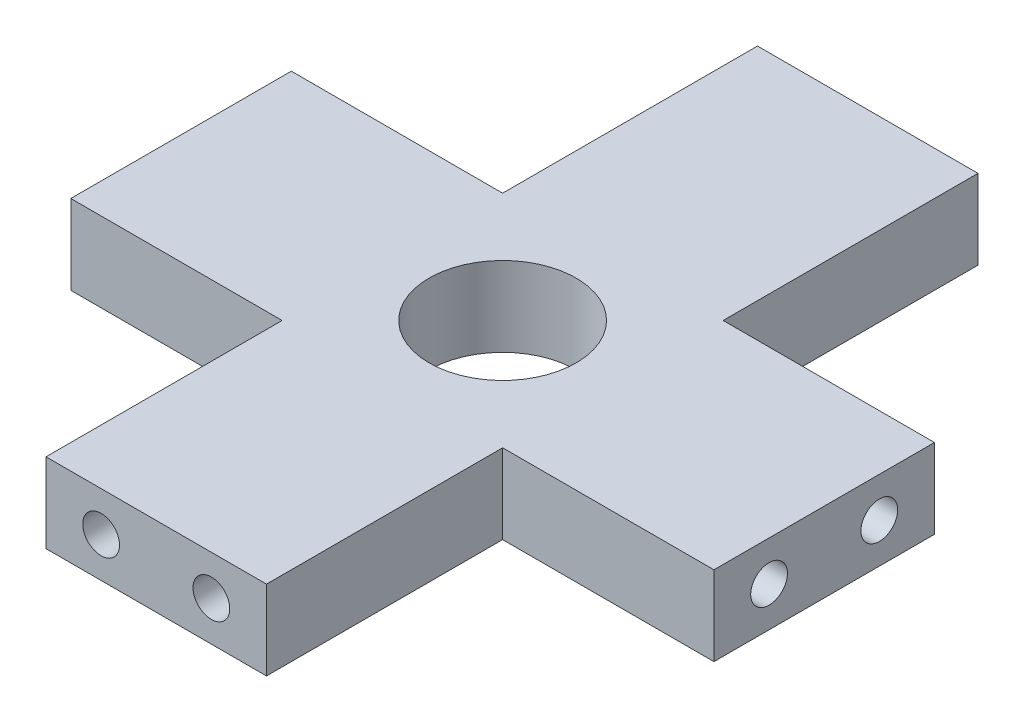
SolidWorks part; units mm, degrees
ref_plane "Front Plane" through (0, 0, 0) normal (0, 0, 1) x (1, 0, 0)
ref_plane "Top Plane" through (0, 0, 0) normal (0, 1, 0) x (1, 0, 0)
ref_plane "Right Plane" through (0, 0, 0) normal (1, 0, 0) x (0, 0, -1)
sketch "Sketch2" plane through (0, 0, 0) normal (0, 1, 0) x (1, 0, 0)
  line L0 (-11.5, 18.85) -> (23.5, 18.85) construction
  line L1 (0, 0) -> (12, 0)
  line L2 (0, 0) -> (0, 12.85)
  line L3 (0, 38.72) -> (12, 38.72)
  line L4 (12, 0) -> (12, 12.85)
  line L5 (6, 0) -> (6, 38.72) construction
  line L6 (-11.5, 24.85) -> (0, 24.85)
  line L7 (-11.5, 24.85) -> (-11.5, 12.85)
  line L8 (-11.5, 12.85) -> (0, 12.85)
  line L9 (23.5, 24.85) -> (23.5, 12.85)
  line L10 (0, 24.85) -> (0, 38.72)
  line L11 (12, 24.85) -> (23.5, 24.85)
  line L12 (12, 24.85) -> (12, 38.72)
  line L13 (12, 12.85) -> (23.5, 12.85)
  circle A0 centre (6, 18.85) radius 4
  dimension "D6" = 8
  dimension "D1" = 38.72
  dimension "D2" = 12
  dimension "D3" = 35
  dimension "D4" = 12
extrude "Boss-Extrude1" add sketch "Sketch2" along normal blind 4.33
sketch "Sketch3" plane through (0, 0, 0) normal (0, 0, 1) x (1, 0, 0)
  line L0 (12, 4.33) -> (12, 0) construction
  line L1 (0, 4.33) -> (0, 0) construction
  line L3 (0, 2.165) -> (12, 2.165) construction
  line L4 (0, 4.33) -> (0, 0) construction
  line L5 (12, 4.33) -> (12, 0) construction
  circle A0 centre (3, 2.165) radius 1
  circle A1 centre (9, 2.165) radius 1
  dimension "D1" = 3
  dimension "D5" = 2
  dimension "D6" = 2
  dimension "D2" = 3
extrude "Cut-Extrude1" cut sketch "Sketch3" against normal blind 5
sketch "Sketch4" plane through (-11.5, 0, 0) normal (-1, 0, 0) x (0, 0, 1)
  line L0 (-12.85, 4.33) -> (-12.85, 0) construction
  line L1 (-24.85, 4.33) -> (-24.85, 0) construction
  line L3 (-24.85, 2.165) -> (-12.85, 2.165) construction
  line L4 (-12.85, 4.33) -> (-12.85, 0) construction
  circle A0 centre (-21.85, 2.165) radius 1
  circle A1 centre (-15.85, 2.165) radius 1
  dimension "D1" = 3
  dimension "D5" = 2
  dimension "D6" = 2
  dimension "D2" = 3
extrude "Cut-Extrude2" cut sketch "Sketch4" against normal blind 5
sketch "Sketch5" plane through (0, 0, -38.72) normal (0, 0, -1) x (-1, 0, 0)
  line L0 (0, 4.33) -> (0, 0) construction
  line L1 (-12, 4.33) -> (-12, 0) construction
  line L3 (-12, 2.165) -> (0, 2.165) construction
  line L4 (-12, 4.33) -> (-12, 0) construction
  circle A0 centre (-9, 2.165) radius 1
  circle A1 centre (-3, 2.165) radius 1
  dimension "D1" = 3
  dimension "D5" = 2
  dimension "D6" = 2
  dimension "D2" = 3
extrude "Cut-Extrude3" cut sketch "Sketch5" against normal blind 5
sketch "Sketch6" plane through (23.5, 0, 0) normal (1, 0, 0) x (0, 0, -1)
  line L0 (24.85, 4.33) -> (24.85, 0) construction
  line L1 (12.85, 4.33) -> (12.85, 0) construction
  line L3 (12.85, 2.165) -> (24.85, 2.165) construction
  line L4 (12.85, 4.33) -> (12.85, 0) construction
  line L5 (24.85, 4.33) -> (24.85, 0) construction
  circle A0 centre (15.85, 2.165) radius 1
  circle A1 centre (21.85, 2.165) radius 1
  dimension "D1" = 3
  dimension "D5" = 2
  dimension "D6" = 2
  dimension "D2" = 3
extrude "Cut-Extrude4" cut sketch "Sketch6" against normal blind 5
sketch "Sketch7" plane through (-11.5, 0, 0) normal (-1, 0, 0) x (0, 0, 1)
